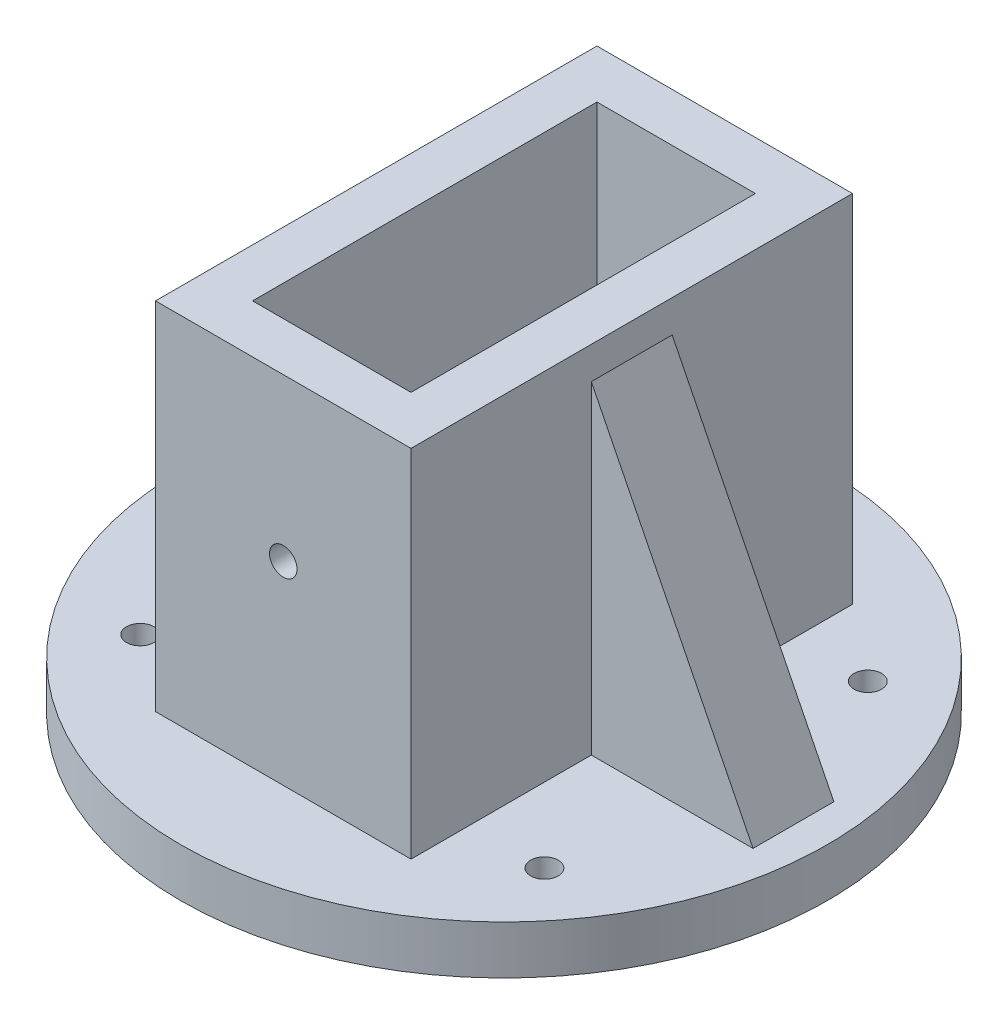
SolidWorks part; units mm, degrees
ref_plane "Alzado" through (0, 0, 0) normal (0, 0, 1) x (1, 0, 0)
ref_plane "Planta" through (0, 0, 0) normal (0, 1, 0) x (1, 0, 0)
ref_plane "Vista lateral" through (0, 0, 0) normal (1, 0, 0) x (0, 0, -1)
sketch "Croquis1" plane through (0, 0, 0) normal (0, 1, 0) x (1, 0, 0)
  line L1 (-9.8, -21.3) -> (9.8, -21.3)
  line L2 (-9.8, -21.3) -> (-9.8, 21.3)
  line L3 (-9.8, 21.3) -> (9.8, 21.3)
  line L4 (9.8, -21.3) -> (9.8, 21.3)
  line L5 (-9.8, -21.3) -> (9.8, 21.3) construction
  line L6 (-9.8, 21.3) -> (9.8, -21.3) construction
  line L7 (15.8, -27.3) -> (-15.8, -27.3)
  line L8 (15.8, -27.3) -> (15.8, 27.3)
  line L9 (15.8, 27.3) -> (-15.8, 27.3)
  line L10 (-15.8, -27.3) -> (-15.8, 27.3)
  line L11 (15.8, -27.3) -> (-15.8, 27.3) construction
  line L12 (15.8, 27.3) -> (-15.8, -27.3) construction
  point P0 (0, 0)
  point P6 (0, 0)
  dimension "D1" = 19.6
  dimension "D2" = 42.6
  dimension "D3" = 6
  dimension "D4" = 6
extrude "Saliente-Extruir1" add sketch "Croquis1" along normal blind 50
sketch "Croquis2" plane through (0, 0, 0) normal (0, -1, 0) x (-1, 0, 0)
  circle A0 centre (0, 0) radius 40
  dimension "D1" = 80
extrude "Saliente-Extruir2" add sketch "Croquis2" against normal blind 6
sketch "Croquis3" plane through (0, 0, 0) normal (0, 0, 1) x (1, 0, 0)
  line L0 (-15.8, 46) -> (-35.8, 6)
  line L1 (-15.8, 50) -> (-15.8, 6) construction
  line L2 (40, 6) -> (-40, 6) construction
  line L5 (15.8, 6) -> (-15.8, 6) construction
  point P12 (0, 0)
  dimension "D1" = 40
  dimension "D2" = 20
rib "Nervio4" sketch "Croquis3" sketch "Croquis3" thickness 10 extrusion direction parallel to sketch draft on no parameters "D1"=10
mirror "Simetría1" about plane through (0, 0, 0) normal (1, 0, 0) of "Nervio4"
sketch "Croquis4" plane through (0, 6, 0) normal (0, 1, 0) x (1, 0, 0)
  line L1 (25, -20) -> (-25, -20) construction
  line L2 (25, -20) -> (25, 20) construction
  line L3 (25, 20) -> (-25, 20) construction
  line L4 (-25, -20) -> (-25, 20) construction
  line L5 (25, -20) -> (-25, 20) construction
  line L6 (25, 20) -> (-25, -20) construction
  circle A0 centre (-25, 20) radius 1.7
  circle A1 centre (-25, -20) radius 1.7
  circle A2 centre (25, -20) radius 1.7
  circle A3 centre (25, 20) radius 1.7
  point P0 (-21.7309, -28.8311)
  point P8 (0, 0)
  point P14 (-22.484, 29.5842)
  dimension "D1" = 3.4
  dimension "D2" = 50
  dimension "D3" = 40
extrude "Cortar-Extruir1" cut sketch "Croquis4" against normal blind 10
sketch "Croquis5" plane through (0, 0, 27.3) normal (0, 0, 1) x (1, 0, 0)
  circle A0 centre (0, 30) radius 1.7
  point P2 (0, 0)
  dimension "D1" = 3.4
  dimension "D2" = 30
extrude "Cortar-Extruir2" cut sketch "Croquis5" against normal blind 60
